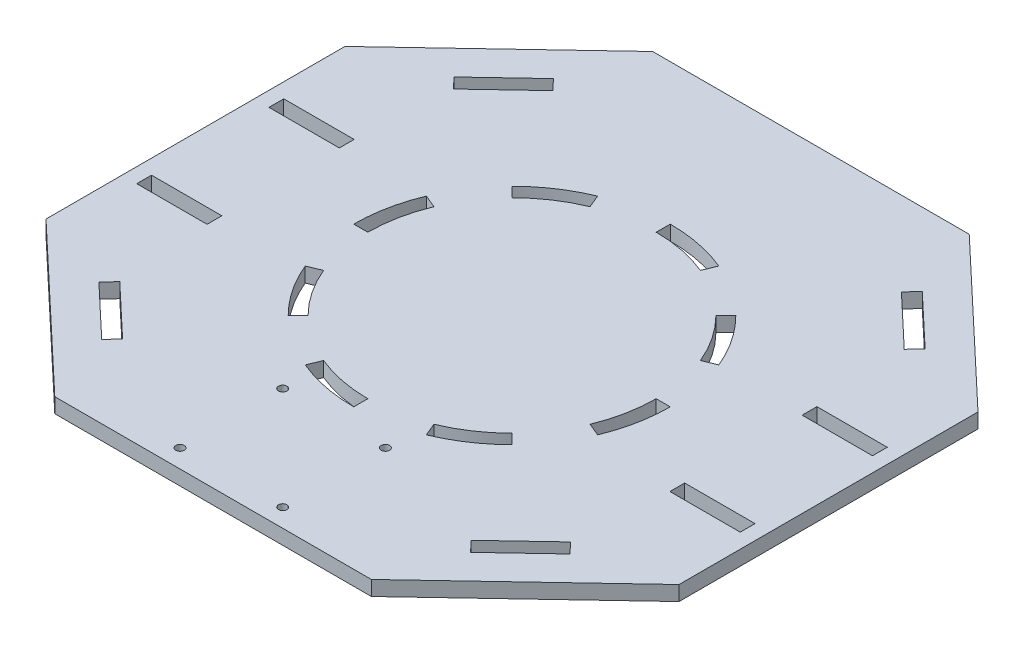
SolidWorks part; units mm, degrees
ref_plane "Front Plane" through (0, 0, 0) normal (0, 0, 1) x (1, 0, 0)
ref_plane "Top Plane" through (0, 0, 0) normal (0, 1, 0) x (1, 0, 0)
ref_plane "Right Plane" through (0, 0, 0) normal (1, 0, 0) x (0, 0, -1)
sketch "Sketch1" plane through (0, 0, 0) normal (0, 1, 0) x (1, 0, 0)
  line L1 (0, 0) -> (228.6, 0)
  line L2 (0, 0) -> (0, 215.9)
  line L3 (0, 215.9) -> (228.6, 215.9)
  line L4 (228.6, 0) -> (228.6, 215.9)
  dimension "D1" = 228.6
  dimension "D2" = 215.9
extrude "Boss-Extrude1" add sketch "Sketch1" along normal blind 5.334 contours L3 L4 L1 L2
sketch "Sketch14" plane through (0, 5.334, 0) normal (0, 1, 0) x (1, 0, 0)
  line L1 (0, 215.9) -> (228.6, 215.9) construction
  line L2 (0, 0) -> (228.6, 0) construction
  line L3 (0, 161.925) -> (228.6, 161.925) construction
  line L4 (0, 0) -> (0, 215.9) construction
  line L5 (228.6, 0) -> (228.6, 215.9) construction
  line L6 (0, 53.975) -> (228.6, 53.975) construction
  line L7 (57.15, 215.9) -> (57.15, 0) construction
  line L8 (171.45, 215.9) -> (171.45, 0) construction
sketch "Sketch13" plane through (0, 5.334, 0) normal (0, 1, 0) x (1, 0, 0)
  line L0 (0, 107.95) -> (228.6, 107.95) construction
  line L1 (0, 0) -> (0, 215.9) construction
  line L2 (228.6, 0) -> (228.6, 215.9) construction
  line L3 (0, 215.9) -> (0, 161.925)
  line L4 (0, 161.925) -> (57.15, 215.9)
  line L5 (57.15, 215.9) -> (0, 215.9)
  line L6 (114.3, 215.9) -> (114.3, 0) construction
  line L7 (0, 215.9) -> (228.6, 215.9) construction
  line L8 (0, 0) -> (228.6, 0) construction
  line L9 (228.6, 161.925) -> (171.45, 215.9)
  line L10 (228.6, 215.9) -> (228.6, 161.925)
  line L11 (171.45, 215.9) -> (228.6, 215.9)
  line L12 (228.6, 0) -> (228.6, 53.975)
  line L13 (171.45, 0) -> (228.6, 0)
  line L14 (228.6, 53.975) -> (171.45, 0)
  line L15 (0, 53.975) -> (57.15, 0)
  line L16 (0, 0) -> (0, 53.975)
  line L17 (57.15, 0) -> (0, 0)
sketch "Sketch6" plane through (0, 5.334, 0) normal (0, 1, 0) x (1, 0, 0)
  line L0 (114.3, 215.9) -> (114.3, 0) construction
  line L1 (0, 215.9) -> (228.6, 215.9) construction
  line L2 (0, 0) -> (228.6, 0) construction
  line L3 (0, 107.95) -> (228.6, 107.95) construction
  line L4 (0, 0) -> (0, 215.9) construction
  line L5 (228.6, 0) -> (228.6, 215.9) construction
  line L6 (228.6, 215.9) -> (0, 0) construction
  line L7 (0, 215.9) -> (228.6, 0) construction
  line L10 (114.3, 160.02) -> (114.3, 165.1)
  line L12 (136.1704, 160.7497) -> (134.2263, 156.0564)
  circle A0 centre (114.3, 107.95) radius 52.07
  arc A2 (114.3, 160.02) -> (152.1556, 143.7025) centre (114.3, 107.95) cw
  arc A3 (114.3, 165.1) -> (136.1704, 160.7497) centre (114.3, 107.95) cw
  arc A4 (114.3, 160.02) -> (134.168, 156.0805) centre (114.3, 107.95) cw
  dimension "D2" = 57.15
  dimension "D1" = 5.08
sketch "Sketch8" plane through (0, 5.334, 0) normal (0, 1, 0) x (1, 0, 0)
  line L0 (0, 107.95) -> (228.6, 107.95) construction
  line L1 (5.334, 134.493) -> (30.734, 134.493)
  line L2 (5.334, 134.493) -> (5.334, 129.159)
  line L3 (5.334, 129.159) -> (30.734, 129.159)
  line L4 (30.734, 134.493) -> (30.734, 129.159)
  line L5 (0, 0) -> (0, 215.9) construction
  line L6 (228.6, 0) -> (228.6, 215.9) construction
  line L11 (114.3, 215.9) -> (114.3, 0) construction
  line L12 (0, 215.9) -> (228.6, 215.9) construction
  line L13 (0, 0) -> (228.6, 0) construction
  line L18 (223.266, 129.159) -> (197.866, 129.159)
  line L19 (197.866, 134.493) -> (197.866, 129.159)
  line L20 (223.266, 134.493) -> (197.866, 134.493)
  line L21 (223.266, 134.493) -> (223.266, 129.159)
  line L22 (223.266, 81.407) -> (223.266, 86.741)
  line L23 (223.266, 81.407) -> (197.866, 81.407)
  line L24 (197.866, 81.407) -> (197.866, 86.741)
  line L25 (223.266, 86.741) -> (197.866, 86.741)
  line L26 (5.334, 86.741) -> (30.734, 86.741)
  line L27 (30.734, 81.407) -> (30.734, 86.741)
  line L28 (5.334, 81.407) -> (30.734, 81.407)
  line L29 (5.334, 81.407) -> (5.334, 86.741)
  dimension "MotorMount1" = 25.4
  dimension "D2" = 5.334
  dimension "D1" = 21.209
  dimension "D5" = 5.334
extrude "Cut-Extrude2" cut sketch "Sketch8" against normal through all contours L2 L1 L4 L3 | L25 L24 L23 L22 | L18 L19 L20 L21 | L26 L27 L28 L29
sketch "Sketch11" plane through (0, 5.334, 0) normal (0, 1, 0) x (1, 0, 0)
  line L0 (114.3, 215.9) -> (114.3, 0) construction
  line L1 (0, 215.9) -> (228.6, 215.9) construction
  line L2 (0, 0) -> (228.6, 0) construction
  line L3 (92.71, 25.146) -> (135.89, 25.146) construction
  circle A0 centre (95.758, 6.604) radius 1.524
  circle A1 centre (132.842, 6.604) radius 1.524
  circle A2 centre (132.842, 43.688) radius 1.524
  circle A3 centre (95.758, 43.688) radius 1.524
extrude "Cut-Extrude4" cut sketch "Sketch11" against normal through all
extrude "Cut-Extrude5" cut sketch "Sketch13" against normal through all
extrude "Cut-Extrude6" cut sketch "Sketch6" against normal through all contours A3 L10 A2 A0 L12
pattern_circular "CirPattern1" count 8 over 360 about axis through (114.3, 0, -107.95) along (0, 1, 0) of "Cut-Extrude6"
sketch "Sketch16" plane through (0, 5.334, 0) normal (0, 1, 0) x (1, 0, 0)
  line L0 (114.3, 215.9) -> (114.3, 0) construction
  line L1 (57.15, 215.9) -> (171.45, 215.9) construction
  line L2 (57.15, 0) -> (171.45, 0) construction
  line L3 (0, 107.95) -> (228.6, 107.95) construction
  line L4 (0, 53.975) -> (0, 161.925) construction
  line L5 (228.6, 53.975) -> (228.6, 161.925) construction
  line L6 (180.8938, 189.5121) -> (199.3599, 172.0719)
  line L16 (180.8938, 189.5121) -> (177.2314, 185.6342)
  line L17 (199.3599, 172.0719) -> (195.6975, 168.194)
  line L18 (177.2314, 185.6342) -> (195.6975, 168.194)
  line L19 (171.45, 215.9) -> (228.6, 161.925) construction
  line L20 (47.7062, 189.5121) -> (51.3686, 185.6342)
  line L21 (51.3686, 185.6342) -> (32.9025, 168.194)
  line L22 (29.2401, 172.0719) -> (32.9025, 168.194)
  line L23 (47.7062, 189.5121) -> (29.2401, 172.0719)
  line L24 (47.7062, 26.3879) -> (29.2401, 43.8281)
  line L25 (29.2401, 43.8281) -> (32.9025, 47.706)
  line L26 (51.3686, 30.2658) -> (32.9025, 47.706)
  line L27 (47.7062, 26.3879) -> (51.3686, 30.2658)
  line L28 (180.8938, 26.3879) -> (177.2314, 30.2658)
  line L29 (177.2314, 30.2658) -> (195.6975, 47.706)
  line L30 (199.3599, 43.8281) -> (195.6975, 47.706)
  line L31 (180.8938, 26.3879) -> (199.3599, 43.8281)
  dimension "D2" = 5.334
  dimension "D1" = 12.7
  dimension "D3" = 25.4
extrude "Cut-Extrude7" cut sketch "Sketch16" against normal through all
equation "\"GMaterial\" = 0.21in"
equation "\"MDF\"= 0.21in"
equation "\"Foamcore\"= 0.2in"
equation "\"D1@Boss-Extrude1\"=\"GMaterial\""
equation "\"D2@Sketch8\"=\"GMaterial\""
equation "\"D1@Sketch8\"=1.67/2"
equation "\"D5@Sketch8\"=\"GMaterial\""
equation "\"D1@Sketch6\"=\"Foamcore\""
equation "\"D2@Sketch16\"=\"GMaterial\""
